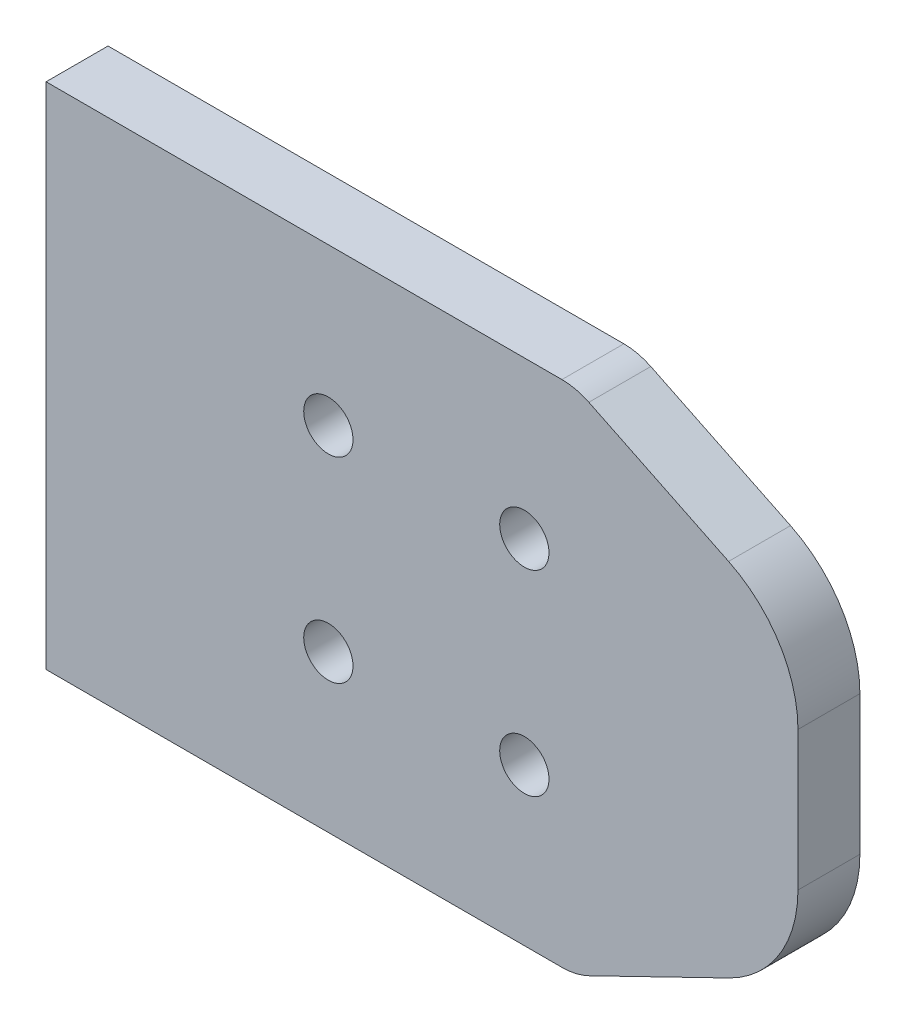
SolidWorks part; units mm, degrees
ref_plane "Front Plane" through (0, 0, 0) normal (0, 0, 1) x (1, 0, 0)
ref_plane "Top Plane" through (0, 0, 0) normal (0, 1, 0) x (1, 0, 0)
ref_plane "Right Plane" through (0, 0, 0) normal (1, 0, 0) x (0, 0, -1)
sketch "Sketch1" plane through (0, 0, 0) normal (0, 0, 1) x (1, 0, 0)
  line L1 (-90.9414, 34.3762) -> (31.0586, 34.3762)
  line L2 (-90.9414, 34.3762) -> (-90.9414, -48.2238)
  line L3 (-90.9414, -48.2238) -> (31.0586, -48.2238)
  line L4 (31.0586, 34.3762) -> (31.0586, -48.2238)
  dimension "D1" = 82.6
  dimension "D2" = 122
extrude "Extrude1" add sketch "Sketch1" along normal blind 10.05
sketch "Sketch2" plane through (0, 0, 0) normal (0, 0, -1) x (-1, 0, 0)
  line L0 (90.9414, 34.3762) -> (90.9414, -48.2238) construction
  line L1 (-31.0586, 34.3762) -> (90.9414, 34.3762) construction
  line L3 (90.9414, -48.2238) -> (-31.0586, -48.2238) construction
  circle A0 centre (45.1414, 8.9762) radius 4
  circle A1 centre (45.1414, -22.8238) radius 4
  circle A2 centre (13.3414, 8.9762) radius 4
  circle A3 centre (13.3414, -22.8238) radius 4
  dimension "D1" = 8
  dimension "D4" = 8
  dimension "D6" = 8
  dimension "D9" = 8
  dimension "D10" = 25.4
  dimension "D2" = 45.8
  dimension "D3" = 25.4
  dimension "D5" = 31.8
  dimension "D7" = 25.4
  dimension "D8" = 31.8
  dimension "D11" = 31.8
  dimension "D12" = 45.8
extrude "Extrude2" cut sketch "Sketch2" against normal through all
sketch "Sketch3" plane through (0, 0, 0) normal (0, 0, -1) x (-1, 0, 0)
  line L0 (4.9414, 34.3762) -> (-31.0586, 16.8762)
  line L1 (-31.0586, 34.3762) -> (90.9414, 34.3762) construction
  line L2 (-31.0586, -48.2238) -> (-31.0586, 34.3762) construction
  line L3 (-31.0586, 16.8762) -> (-39.4579, 42.9341)
  line L4 (-39.4579, 42.9341) -> (4.9414, 34.3762)
  line L6 (-31.0586, -30.7238) -> (-39.4579, -56.7817)
  line L7 (-39.4579, -56.7817) -> (4.9414, -48.2238)
  line L8 (4.9414, -48.2238) -> (-31.0586, -30.7238)
  dimension "D1" = 17.5
  dimension "D2" = 36
extrude "Extrude3" cut sketch "Sketch3" against normal through all
fillet "Fillet1" radius 10 2 edges at (-4.9414, -48.2238, 5.025) (-4.9414, 34.3762, 5.025)
fillet "Fillet2" radius 20 2 edges at (31.0586, -30.7238, 5.025) (31.0586, 16.8762, 5.025)
